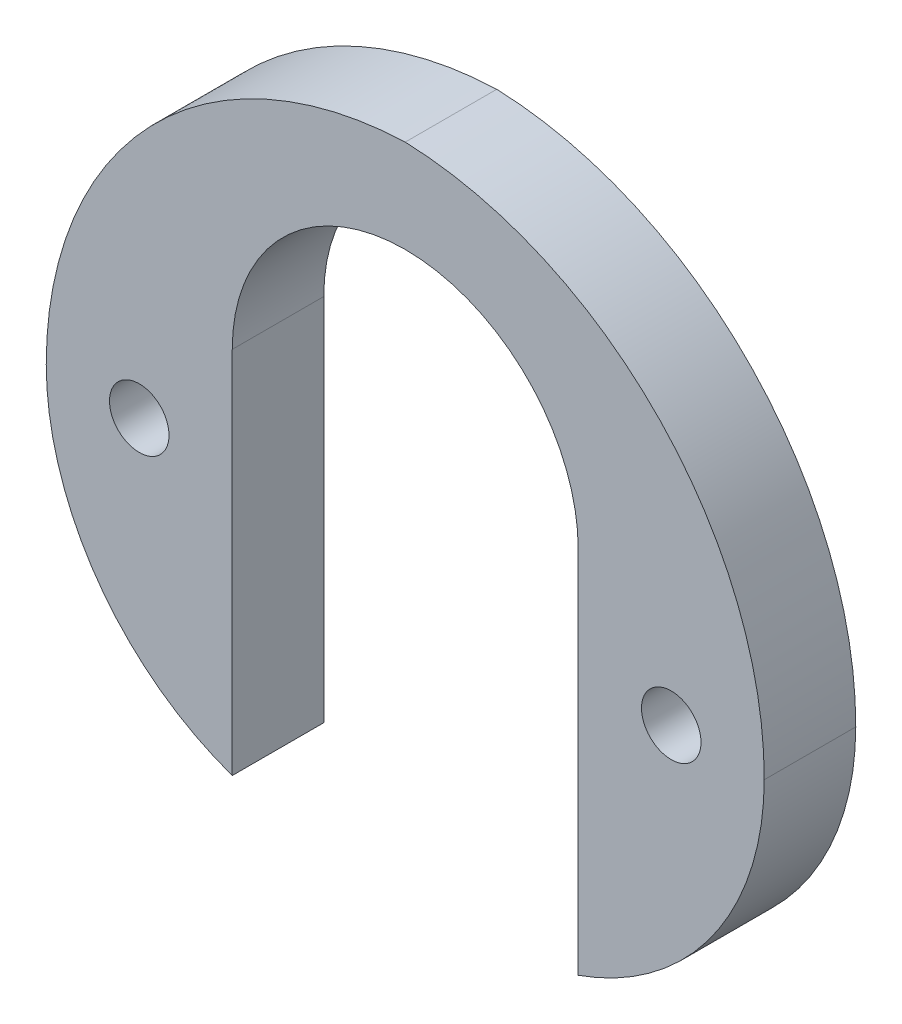
SolidWorks part; units mm, degrees
ref_plane "Alzado" through (0, 0, 0) normal (0, 0, 1) x (1, 0, 0)
ref_plane "Planta" through (0, 0, 0) normal (0, 1, 0) x (1, 0, 0)
ref_plane "Vista lateral" through (0, 0, 0) normal (1, 0, 0) x (0, 0, -1)
sketch "Croquis1" plane through (0, 0, 0) normal (0, 0, 1) x (1, 0, 0)
  line L0 (0, 3.6195) -> (0, -3.6195) construction
  line L1 (-2.7305, 0) -> (2.7305, 0) construction
  line L2 (-2.7305, 9.525) -> (2.7305, 9.525)
  line L3 (-2.7305, -9.525) -> (2.7305, -9.525)
  line L6 (0, 3.6195) -> (0, -3.6195) construction
  line L7 (5.9055, 3.6195) -> (5.9055, -3.6195)
  line L8 (-5.9055, 3.6195) -> (-5.9055, -3.6195)
  line L9 (5.9055, -3.6195) -> (5.9055, -8.9803)
  line L10 (-5.9055, -3.6195) -> (-5.9055, -8.9803)
  circle A0 centre (0, 3.6195) radius 5.9055
  circle A1 centre (0, -3.6195) radius 5.9055
  arc A3 (-2.7305, 9.525) -> (-2.7305, -9.525) centre (-2.7305, 0) ccw
  arc A4 (2.7305, -9.525) -> (2.7305, 9.525) centre (2.7305, 0) ccw
  arc A5 (-12.2555, 0) -> (0, 12.7) centre (0.4526, 0) cw
  arc A7 (0, 12.7) -> (12.2555, -0.0233) centre (-0.4445, 0.0078) cw
  arc A8 (5.9055, 3.6195) -> (-5.9055, 3.6195) centre (0, 3.6195) ccw
  arc A9 (-5.9055, -3.6195) -> (5.9055, -3.6195) centre (0, -3.6195) ccw
  circle A10 centre (-9.0805, 0) radius 1.016
  circle A11 centre (9.0805, 0) radius 1.016
  circle A12 centre (9.0805, 0) radius 1.016
  point P7 (0, 0)
  point P12 (0, 0)
  dimension "D1" = 9.525
  dimension "D2" = 2.032
  dimension "D3" = 6.35
  dimension "D4" = 12.7
  dimension "D5" = 11.811
  dimension "D6" = 3.175
  dimension "D7" = 3.175
extrude "Saliente-Extruir1" add sketch "Croquis1" along normal blind 3.1242 contours L2 A3 L10 L8 A0 A10 | A7 A5 A3 L2 A4 | L9 A4 L2 A0 L7 A11
